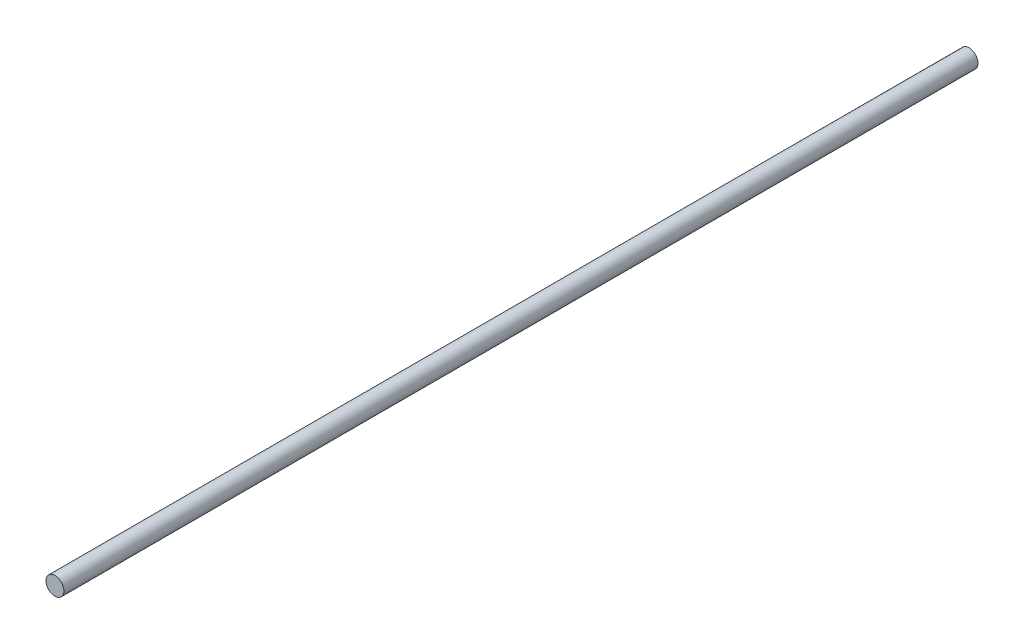
SolidWorks part; units mm, degrees
ref_plane "Front Plane" through (0, 0, 0) normal (0, 0, 1) x (1, 0, 0)
ref_plane "Top Plane" through (0, 0, 0) normal (0, 1, 0) x (1, 0, 0)
ref_plane "Right Plane" through (0, 0, 0) normal (1, 0, 0) x (0, 0, -1)
sketch "Sketch1" plane through (0, 0, 0) normal (0, 0, 1) x (1, 0, 0)
  circle A0 centre (0, 0) radius 5
  dimension "D1" = 10
extrude "Boss-Extrude4" add sketch "Sketch1" along normal blind 510
